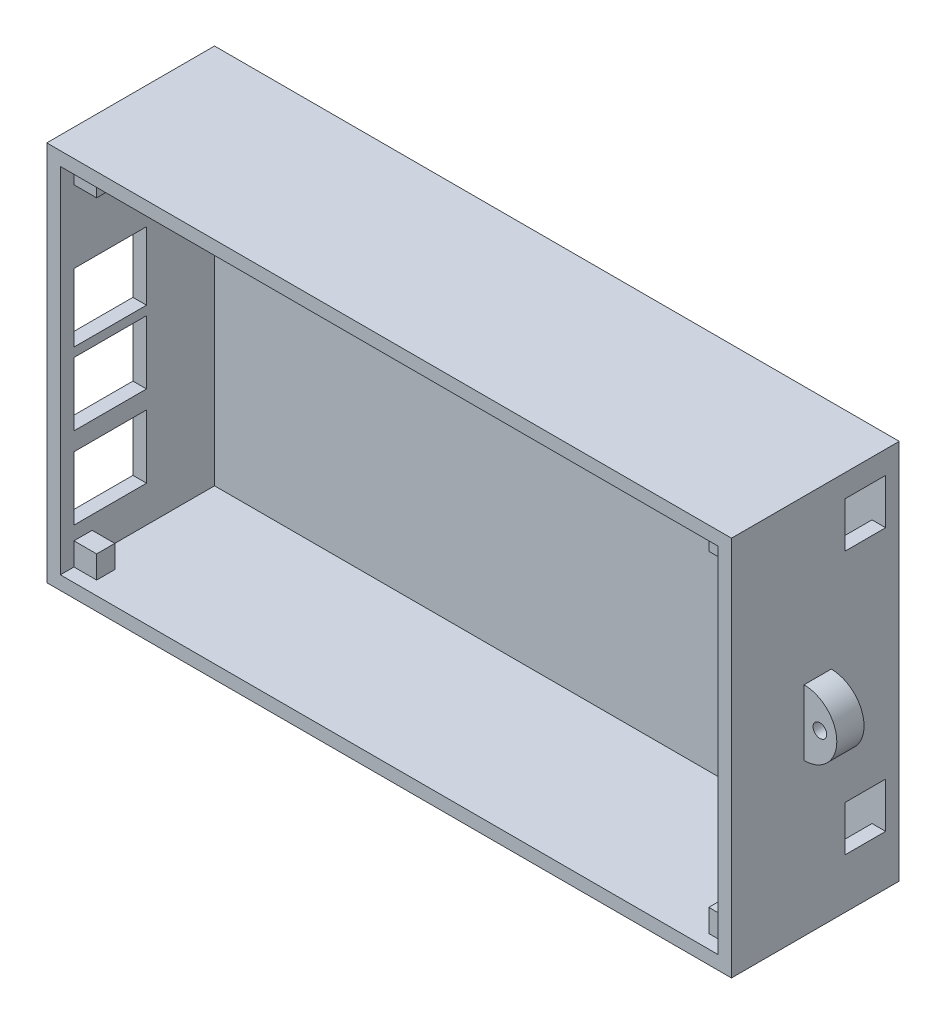
SolidWorks part; units mm, degrees
ref_plane "Front Plane" through (0, 0, 0) normal (0, 0, 1) x (1, 0, 0)
ref_plane "Top Plane" through (0, 0, 0) normal (0, 1, 0) x (1, 0, 0)
ref_plane "Right Plane" through (0, 0, 0) normal (1, 0, 0) x (0, 0, -1)
sketch "Sketch1" plane through (0, 0, 0) normal (0, 0, 1) x (1, 0, 0)
  line L1 (75.5, 42) -> (-75.5, 42)
  line L2 (75.5, 42) -> (75.5, -42)
  line L3 (75.5, -42) -> (-75.5, -42)
  line L4 (-75.5, 42) -> (-75.5, -42)
  line L5 (0, -42) -> (0, 42) construction
  line L6 (75.5, 0) -> (-75.5, 0) construction
  point P0 (0, 0)
extrude "Boss-Extrude1" add sketch "Sketch1" along normal blind 37
sketch "Sketch3" plane through (0, 0, 37) normal (0, 0, 1) x (1, 0, 0)
  line L1 (-72.5, 39) -> (72.5, 39)
  line L2 (-72.5, 39) -> (-72.5, -39)
  line L3 (-72.5, -39) -> (72.5, -39)
  line L4 (72.5, 39) -> (72.5, -39)
  line L5 (0, -39) -> (0, 39) construction
  line L6 (-72.5, 0) -> (72.5, 0) construction
  point P0 (0, 0)
extrude "Cut-Extrude3" cut sketch "Sketch3" against normal blind 34
sketch "Sketch8" plane through (-75.5, 0, 0) normal (-1, 0, 0) x (0, 0, 1)
  line L0 (37, 42) -> (37, -42) construction
  line L1 (18, -31) -> (37, -31)
  line L2 (18, -31) -> (18, -17)
  line L3 (18, -17) -> (37, -17)
  line L4 (37, -31) -> (37, -17)
  point P6 (0, 0)
  point P7 (0, 0)
  point P8 (0, 0)
  point P9 (0, 0)
  point P10 (0, 0)
  point P11 (0, 0)
extrude "Cut-Extrude4" cut sketch "Sketch8" against normal blind 3
sketch "Sketch9" plane through (-75.5, 0, 0) normal (-1, 0, 0) x (0, 0, 1)
  line L1 (18, 1) -> (37, 1)
  line L2 (18, 1) -> (18, -13)
  line L3 (18, -13) -> (37, -13)
  line L4 (37, 1) -> (37, -13)
  point P4 (0, 0)
  point P5 (0, 0)
  point P6 (0, 0)
  point P7 (0, 0)
  point P8 (0, 0)
  point P9 (0, 0)
  point P10 (0, 0)
  point P11 (0, 0)
  point P12 (0, 0)
  point P13 (0, 0)
  point P14 (0, 0)
extrude "Cut-Extrude5" cut sketch "Sketch9" against normal blind 3
sketch "Sketch11" plane through (75.5, 0, 0) normal (1, 0, 0) x (0, 0, -1)
  line L1 (-3, 37) -> (-12, 37)
  line L2 (-3, 37) -> (-3, 27)
  line L3 (-3, 27) -> (-12, 27)
  line L4 (-12, 37) -> (-12, 27)
extrude "Cut-Extrude6" cut sketch "Sketch11" against normal blind 3
sketch "Sketch12" plane through (75.5, 0, 0) normal (1, 0, 0) x (0, 0, -1)
  line L1 (-12, -21) -> (-3, -21)
  line L2 (-12, -21) -> (-12, -31)
  line L3 (-12, -31) -> (-3, -31)
  line L4 (-3, -21) -> (-3, -31)
extrude "Cut-Extrude7" cut sketch "Sketch12" against normal blind 3
ref_plane "Plane2" through (0, 0, 18) normal (0, 0, 1) x (1, 0, 0)
sketch "Sketch16" plane through (0, 0, 18) normal (0, 0, 1) x (1, 0, 0)
  line L0 (75.5, 6) -> (75.5, -8.4611)
  arc A0 (75.5, 6) -> (75.5, -8.4611) centre (75.5, -1.2306) cw
extrude "Boss-Extrude2" add sketch "Sketch16" along normal blind 3 and the other way blind 3
sketch "Sketch19" plane through (0, 0, 21) normal (0, 0, 1) x (1, 0, 0)
  circle A0 centre (79, -1) radius 1.5
extrude "Cut-Extrude8" cut sketch "Sketch19" against normal blind 6
sketch "Sketch20" plane through (-75.5, 0, 0) normal (-1, 0, 0) x (0, 0, 1)
  line L0 (18, -13) -> (37, -13) construction
  line L1 (37, 1) -> (34, 1)
  line L2 (37, 1) -> (37, -13)
  line L3 (37, -13) -> (34, -13)
  line L4 (34, 1) -> (34, -13)
extrude "Boss-Extrude3" add sketch "Sketch20" against normal blind 3
sketch "Sketch21" plane through (-75.5, 0, 0) normal (-1, 0, 0) x (0, 0, 1)
  line L0 (18, -31) -> (37, -31) construction
  line L1 (37, -17) -> (34, -17)
  line L2 (37, -17) -> (37, -31)
  line L3 (37, -31) -> (34, -31)
  line L4 (34, -17) -> (34, -31)
extrude "Boss-Extrude4" add sketch "Sketch21" against normal blind 3
sketch "Sketch23" plane through (-75.5, 0, 0) normal (-1, 0, 0) x (0, 0, 1)
  line L1 (18, 18) -> (34, 18)
  line L2 (18, 18) -> (18, 3)
  line L3 (18, 3) -> (34, 3)
  line L4 (34, 18) -> (34, 3)
  point P4 (0, 0)
  point P5 (0, 0)
  point P6 (0, 0)
  point P7 (0, 0)
  point P8 (0, 0)
  point P9 (0, 0)
  point P10 (0, 0)
  point P11 (0, 0)
  point P12 (0, 0)
  point P13 (0, 0)
  point P14 (0, 0)
  point P15 (0, 0)
  point P16 (0, 0)
  point P17 (0, 0)
extrude "Cut-Extrude9" cut sketch "Sketch23" against normal blind 3
sketch "Sketch28" plane through (72.5, 0, 0) normal (-1, 0, 0) x (0, 0, 1)
  line L0 (3, -39) -> (37, -39) construction
  line L1 (34, -39) -> (30, -39)
  line L2 (34, -39) -> (34, -34)
  line L3 (34, -34) -> (30, -34)
  line L4 (30, -39) -> (30, -34)
  point P6 (0, 0)
  point P7 (0, 0)
  point P8 (0, 0)
  point P9 (0, 0)
  point P10 (0, 0)
  point P11 (0, 0)
  point P12 (0, 0)
  point P13 (0, 0)
  point P14 (0, 0)
  point P15 (0, 0)
  point P16 (0, 0)
extrude "Boss-Extrude5" add sketch "Sketch28" along normal blind 5
mirror "Mirror1" about plane through (0, 0, 0) normal (0, 1, 0) of "Boss-Extrude5"
mirror "Mirror2" about plane through (0, 0, 0) normal (1, 0, 0) of "Boss-Extrude5", "Mirror1"
